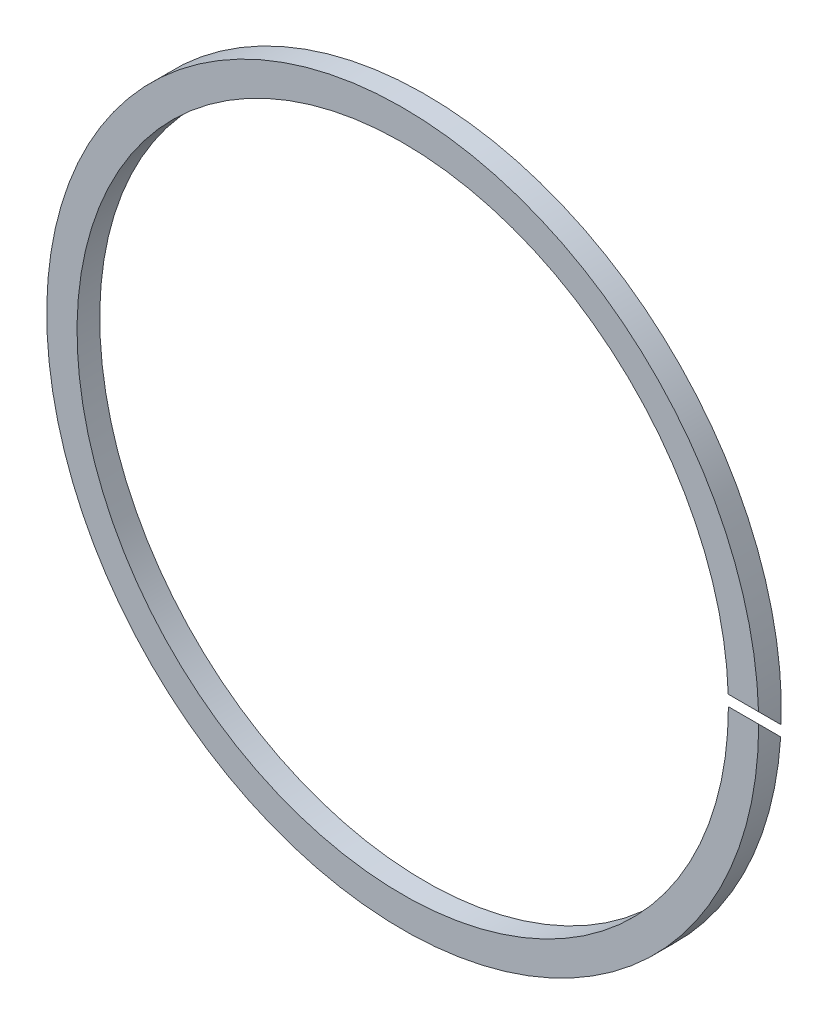
SolidWorks part; units mm, degrees
ref_plane "Front Plane" through (0, 0, 0) normal (0, 0, 1) x (1, 0, 0)
ref_plane "Top Plane" through (0, 0, 0) normal (0, 1, 0) x (1, 0, 0)
ref_plane "Right Plane" through (0, 0, 0) normal (1, 0, 0) x (0, 0, -1)
sketch "Sketch1" plane through (0, 0, 0) normal (0, 0, 1) x (1, 0, 0)
  circle A0 centre (0, 0) radius 47
  circle A1 centre (0, 0) radius 43
  dimension "D1" = 94
  dimension "D2" = 86
extrude "Boss-Extrude1" add sketch "Sketch1" along normal blind 3
sketch "Sketch3" plane through (0, 0, 0) normal (1, 0, 0) x (0, 0, -1)
  line L0 (-3, 0) -> (0, -3)
  line L1 (-3, 47) -> (-3, -47) construction
  line L2 (0, -47) -> (0, 47) construction
  line L3 (-3, 1.4142) -> (0.7071, -2.2929)
  line L4 (-2.2929, 0.7071) -> (0.7071, -2.2929) construction
  line L5 (0, -3) -> (0.7071, -2.2929)
  line L6 (-3, 1.4142) -> (-3, 0)
  dimension "D1" = 135
  dimension "D2" = 1
extrude "Cut-Extrude1" cut sketch "Sketch3" along normal through all
